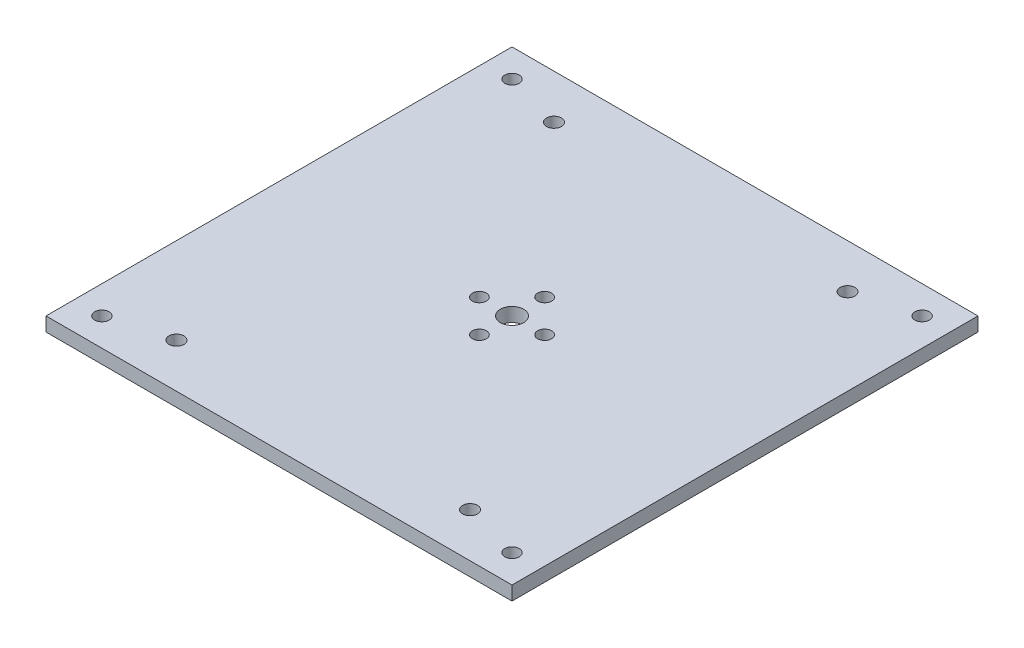
SolidWorks part; units mm, degrees
ref_plane "Front" through (0, 0, 0) normal (0, 0, 1) x (1, 0, 0)
ref_plane "Top" through (0, 0, 0) normal (0, 1, 0) x (1, 0, 0)
ref_plane "Right" through (0, 0, 0) normal (1, 0, 0) x (0, 0, -1)
sketch "Croquis1" plane through (0, 0, 0) normal (0, 1, 0) x (1, 0, 0)
  line L1 (-50, 50) -> (50, 50)
  line L2 (-50, 50) -> (-50, -50)
  line L3 (-50, -50) -> (50, -50)
  line L4 (50, 50) -> (50, -50)
  dimension "D1" = 50
  dimension "D2" = 50
  dimension "D3" = 50
  dimension "D4" = 50
extrude "Saliente-Extruir1" add sketch "Croquis1" along normal blind 3
sketch "Croquis6" plane through (0, 3, 0) normal (0, 1, 0) x (1, 0, 0)
  line L0 (50, 50) -> (-50, 50) construction
  line L1 (-50, 50) -> (-50, -50) construction
  line L2 (50, -50) -> (50, 50) construction
  line L3 (-50, -50) -> (50, -50) construction
  circle A0 centre (-44, 44) radius 1.55
  circle A1 centre (44, 44) radius 1.55
  circle A2 centre (44, -44) radius 1.55
  circle A3 centre (-44, -44) radius 1.55
  dimension "D1" = 3.1
  dimension "D5" = 3.1
  dimension "D9" = 3.1
  dimension "D12" = 3.1
  dimension "D2" = 6
  dimension "D3" = 6
  dimension "D4" = 6
  dimension "D6" = 6
  dimension "D7" = 6
  dimension "D8" = 6
  dimension "D10" = 6
  dimension "D11" = 6
extrude "Cortar-Extruir4" cut sketch "Croquis6" against normal blind 10
sketch "Croquis7" plane through (0, 3, 0) normal (0, 1, 0) x (1, 0, 0)
  line L0 (-50, 50) -> (-50, -50) construction
  line L2 (50, -50) -> (50, 50) construction
  line L3 (50, 50) -> (-50, 50) construction
  line L5 (-50, -50) -> (50, -50) construction
  circle A0 centre (-31.5, 40.5) radius 1.6
  circle A1 centre (31.5, 40.5) radius 1.6
  circle A2 centre (-31.5, -40.5) radius 1.6
  circle A3 centre (31.5, -40.5) radius 1.6
  dimension "D1" = 63
  dimension "D5" = 3.2
  dimension "D6" = 3.2
  dimension "D7" = 3.2
  dimension "D8" = 3.2
  dimension "D2" = 63
  dimension "D3" = 81
  dimension "D4" = 81
  dimension "D9" = 18.5
  dimension "D10" = 18.5
  dimension "D11" = 9.5
  dimension "D12" = 9.5
  dimension "D13" = 9.5
  dimension "D14" = 9.5
extrude "Cortar-Extruir5" cut sketch "Croquis7" against normal blind 10
sketch "Croquis8" plane through (0, 3, 0) normal (0, 1, 0) x (1, 0, 0)
  circle A0 centre (0, 0) radius 2.5
  circle A2 centre (0, 7) radius 1.5
  circle A3 centre (7, 0) radius 1.5
  circle A4 centre (0, -7) radius 1.5
  circle A5 centre (-7, 0) radius 1.5
  dimension "D1" = 5
  dimension "D3" = 3
  dimension "D4" = 3
  dimension "D5" = 3
  dimension "D6" = 3
extrude "Cortar-Extruir6" cut sketch "Croquis8" against normal blind 10
